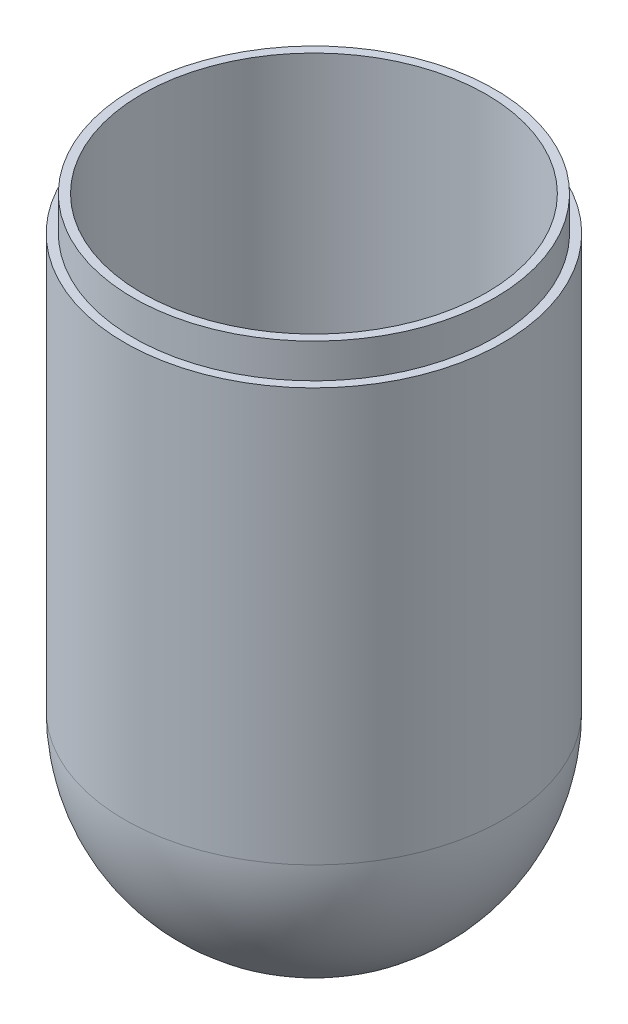
SolidWorks part; units mm, degrees
ref_plane "Front Plane" through (0, 0, 0) normal (0, 0, 1) x (1, 0, 0)
ref_plane "Top Plane" through (0, 0, 0) normal (0, 1, 0) x (1, 0, 0)
ref_plane "Right Plane" through (0, 0, 0) normal (1, 0, 0) x (0, 0, -1)
sketch "Sketch1" plane through (0, 0, 0) normal (0, 0, 1) x (1, 0, 0)
  line L0 (63.5, 0) -> (63.5, 152.4)
  line L1 (63.5, 152.4) -> (66.675, 152.4)
  line L2 (69.85, 152.4) -> (69.85, 0)
  line L3 (0, -63.5) -> (0, -69.85)
  line L7 (69.85, 152.4) -> (69.85, 165.1)
  line L8 (69.85, 165.1) -> (66.675, 165.1)
  line L9 (66.675, 152.4) -> (66.675, 165.1)
  arc A0 (0, -63.5) -> (63.5, 0) centre (0, 0) ccw
  arc A1 (0, -69.85) -> (69.85, 0) centre (0, 0) ccw
  dimension "D3" = 63.5
  dimension "D4" = 12.7
  dimension "D1" = 6.35
  dimension "D2" = 152.4
  dimension "D5" = 3.175
revolve "Revolve1" add sketch "Sketch1" angle 360 about L3
sketch "Sketch3" plane through (0, 165.1, 0) normal (0, 1, 0) x (1, 0, 0)
  circle A0 centre (0, 0) radius 69.85
extrude "Cut-Extrude1" cut sketch "Sketch3" against normal blind 12.7
sketch "Sketch4" plane through (0, 152.4, 0) normal (0, 1, 0) x (1, 0, 0)
  circle A0 centre (0, 0) radius 66.675
  circle A1 centre (0, 0) radius 63.5
  dimension "D1" = 3.175
extrude "Boss-Extrude2" add sketch "Sketch4" along normal blind 12.7
sketch "Sketch5" plane through (0, 165.1, 0) normal (0, 1, 0) x (1, 0, 0)
  circle A0 centre (0, 0) radius 68.2625
  circle A1 centre (0, 0) radius 66.675 construction
  circle A2 centre (0, 0) radius 66.675
  dimension "D1" = 1.5875
extrude "Boss-Extrude3" add sketch "Sketch5" against normal blind 9.525
sketch "Sketch7" plane through (0, 165.1, 0) normal (0, 1, 0) x (1, 0, 0)
  circle A0 centre (0, 0) radius 63.5
  circle A1 centre (0, 0) radius 66.675
  circle A3 centre (0, 0) radius 68.2625
  circle M2 centre (0, 0) radius 68.2625
  dimension "D1" = 3.175
extrude "Cut-Extrude2" cut sketch "Sketch7" against normal blind 1.5875 contours A1 M2
sketch "Sketch12" plane through (0, 163.5125, 0) normal (0, 1, 0) x (1, 0, 0)
  circle A0 centre (0, 0) radius 68.2625
  circle A1 centre (0, 0) radius 66.675
extrude "Cut-Extrude3" cut sketch "Sketch12" against normal blind 7.9375
